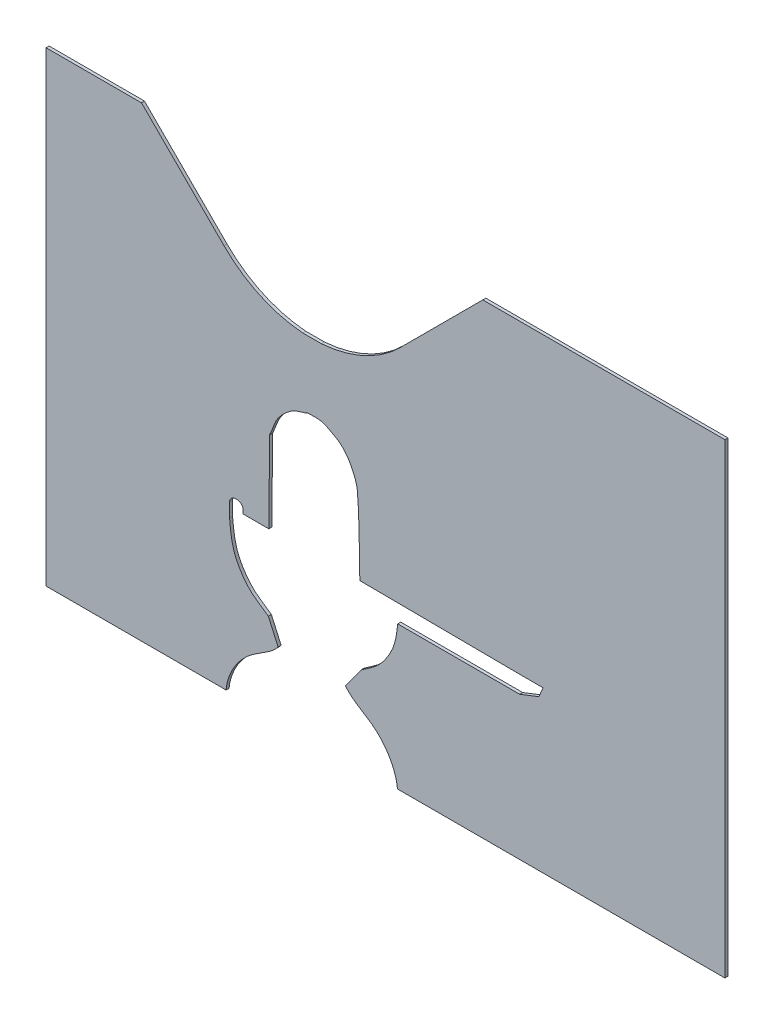
SolidWorks part; units mm, degrees
ref_plane "Front Plane" through (0, 0, 0) normal (0, 0, 1) x (1, 0, 0)
ref_plane "Top Plane" through (0, 0, 0) normal (0, 1, 0) x (1, 0, 0)
ref_plane "Right Plane" through (0, 0, 0) normal (1, 0, 0) x (0, 0, -1)
sketch "Sketch1" plane through (0, 0, 0) normal (0, 0, 1) x (1, 0, 0)
  line L0 (133.3333, 254.5) -> (666.6667, 254.5) construction
  line L1 (133.3333, 254.5) -> (666.6667, 254.5) construction
  line L2 (370.4976, 301.8562) -> (372, 438)
  line L3 (522, 303) -> (789, 301)
  line L5 (584.6436, 11.5928) -> (537.0464, 5.228)
  line L6 (537.0464, 5.228) -> (347.0464, 5.228)
  line L7 (347.0464, 5.228) -> (299.4492, 11.5928)
  line L10 (788.0464, 272.228) -> (585.1554, 272.228)
  line L11 (305.2792, 294.7179) -> (305.2792, 307.6224)
  line L15 (305.2792, 294.7179) -> (305.2792, 284.7179)
  line L22 (788.0464, 272.228) -> (819.9189, 284.7179)
  line L23 (819.9189, 284.7179) -> (827.0328, 301)
  line L24 (827.0328, 301) -> (789, 301)
  line L25 (369.7697, 175.6281) -> (386.0962, 139.3042)
  line L27 (315.2792, 317.6224) -> (317.682, 317.6224)
  line L28 (524.0902, 175.3163) -> (497.9967, 139.3042)
  line L29 (447, 5.228) -> (447, 123.3402) construction
  line L30 (327.682, 307.6224) -> (327.682, 301.8562)
  line L31 (327.682, 301.8562) -> (370.4976, 301.8562)
  line L34 (444.2405, 428) -> (444.2405, 446.7948) construction
  arc A8 (406.6112, 432.934) -> (481.8698, 432.934) centre (444.2405, 573.9572) ccw
  arc A9 (317.682, 317.6224) -> (327.682, 307.6224) centre (317.682, 307.6224) cw
  arc A10 (406.6112, 418.489) -> (481.8698, 418.489) centre (444.2405, 573.9572) ccw
  arc A11 (305.2792, 307.6224) -> (315.2792, 317.6224) centre (315.2792, 307.6224) cw
  arc A12 (406.6112, 432.934) -> (406.6112, 418.489) centre (408.5979, 425.7115) ccw
  arc A13 (481.8698, 432.934) -> (481.8698, 418.489) centre (479.8831, 425.7115) cw
  arc A15 (406.6112, 398) -> (481.8698, 398) centre (444.2405, 539.0232) ccw
  arc A16 (406.6112, 383.5551) -> (481.8698, 383.5551) centre (444.2405, 539.0232) ccw
  arc A17 (406.6112, 398) -> (406.6112, 383.5551) centre (408.5979, 390.7775) ccw
  arc A18 (481.8698, 398) -> (481.8698, 383.5551) centre (479.8831, 390.7775) cw
  arc A19 (406.6112, 363.066) -> (481.8698, 363.066) centre (444.2405, 504.0892) ccw
  arc A20 (406.6112, 348.6211) -> (481.8698, 348.6211) centre (444.2405, 504.0892) ccw
  arc A21 (406.6112, 363.066) -> (406.6112, 348.6211) centre (408.5979, 355.8435) ccw
  arc A22 (481.8698, 363.066) -> (481.8698, 348.6211) centre (479.8831, 355.8435) cw
  spline S0 degree 3 poles (497.9967, 139.3042) (511.7518, 122.1516) (533.2072, 114.7602) (549.1688, 100.4046) (557.8006, 92.6413) (565.3882, 83.5064) (571.3127, 73.5225) (576.9673, 63.9934) (581.1463, 53.4194) (583.4781, 42.5871) (585.6538, 32.4799) (584.2551, 21.9242) (584.6436, 11.5928) knots -0.601085 -0.601085 -0.601085 -0.601085 1 1 1 2 2 2 3 3 3 4 4 4 4
  spline S6 degree 3 poles (524.0902, 175.3163) (534.1328, 182.777) (545.3011, 188.9678) (553.9879, 197.958) (562.3903, 206.6539) (569.2318, 216.9804) (574.5688, 227.831) (581.2804, 241.4764) (583.659, 256.9216) (585.1554, 272.228) knots 0.030911 0.030911 0.030911 0.030911 1 1 1 2 2 2 2.820582 2.820582 2.820582 2.820582
  spline S9 degree 3 poles (372, 438) (377.0706, 448.1412) (379.4614, 459.737) (386, 469) (392.1182, 477.6674) (400.1437, 485.1586) (409, 491) (416.1323, 495.7043) (425.0671, 496.8268) (433, 500) (433.4377, 500.1751) (433.5288, 501.0152) (434, 501) (438.4944, 500.855) (456.988, 503.3404) (466, 498) (474.3605, 493.0456) (483.7936, 489.5201) (491, 483) (498.0695, 476.6038) (503.6725, 468.4948) (508, 460) (512.7848, 450.6076) (517.0638, 440.4993) (518, 430) (521.7619, 387.8131) (520.6667, 345.3333) (522, 303) knots 0 0 0 0 1 1 1 2 2 2 3 3 3 4 4 4 5 5 5 6 6 6 7 7 7 8 8 8 9 9 9 9
  spline S13 degree 3 poles (369.7697, 175.6281) (359.276, 183.4916) (347.4468, 189.8334) (338.2886, 199.2185) (329.7041, 208.0157) (322.698, 218.4783) (317.2186, 229.4811) (308.8213, 246.3434) (306.9517, 265.9548) (305.2792, 284.7179) knots 0 0 0 0 1 1 1 2 2 2 3 3 3 3
  spline S20 degree 3 poles (386.0962, 139.3042) (372.341, 122.1516) (350.8856, 114.7602) (334.924, 100.4046) (326.2922, 92.6413) (318.7046, 83.5064) (312.7801, 73.5225) (307.1255, 63.9934) (302.9465, 53.4194) (300.6147, 42.5871) (298.4391, 32.4799) (299.8377, 21.9242) (299.4492, 11.5928) knots -0.601085 -0.601085 -0.601085 -0.601085 1 1 1 2 2 2 3 3 3 4 4 4 4
  point P21 (320.0752, 796.7868)
  point P22 (444.2405, 639.4617)
  point P24 (385.3282, 418.6761)
  point P25 (503.1529, 418.6761)
  point P27 (560.9295, 796.7868)
  point P31 (440.5024, 886.2654)
  point P36 (315.1479, 786.7868)
  point P37 (440.5024, 886.2654)
  point P38 (568.9564, 790.8228)
  dimension "D2" = 3
  dimension "D4" = 10
  dimension "D5" = 10
extrude "Boss-Extrude1" add sketch "Sketch1" against normal blind 5
sketch "Sketch4" plane through (0, 0, 0) normal (0, 0, 1) x (1, 0, 0)
  line L0 (442.6877, 501.3599) -> (442.6877, 672.663) construction
  line L1 (0, 809.9054) -> (158.6896, 809.9054)
  line L2 (0, 809.9054) -> (0, 34.0489)
  line L3 (0, 34.0489) -> (1129.4723, 34.0489)
  line L4 (1129.4723, 809.9054) -> (1129.4723, 34.0489)
  line L5 (589.4434, 672.663) -> (726.6858, 809.9054)
  line L6 (295.932, 672.663) -> (158.6896, 809.9054)
  line L7 (726.6858, 809.9054) -> (1129.4723, 809.9054)
  line L8 (427.2747, 612.4479) -> (458.1007, 612.4479)
  line L10 (347.0464, 34.0489) -> (537.0464, 34.0489) construction
  arc A0 (295.932, 672.663) -> (427.2747, 612.4479) centre (442.6877, 819.4187) ccw
  arc A1 (458.1007, 612.4479) -> (589.4434, 672.663) centre (442.6877, 819.4187) ccw
  spline S0 degree 3 poles (522, 303) (520.6667, 345.3333) (521.7619, 387.8131) (518, 430) (517.0638, 440.4993) (512.7848, 450.6076) (508, 460) (503.6725, 468.4948) (498.0695, 476.6038) (491, 483) (483.7936, 489.5201) (474.3605, 493.0456) (466, 498) (456.988, 503.3404) (438.4944, 500.855) (434, 501) (433.5288, 501.0152) (433.4377, 500.1751) (433, 500) (425.0671, 496.8268) (416.1323, 495.7043) (409, 491) (400.1437, 485.1586) (392.1182, 477.6674) (386, 469) (379.4614, 459.737) (377.0706, 448.1412) (372, 438) knots 0 0 0 0 1 1 1 2 2 2 3 3 3 4 4 4 5 5 5 6 6 6 7 7 7 8 8 8 9 9 9 9 construction
extrude "Boss-Extrude2" add sketch "Sketch4" against normal blind 5 separate body
surface "Surface-Offset1" parameters "D1"=0
other "SurfaceCut1"
sketch "Sketch5" plane through (0, 0, -5) normal (0, 0, -1) x (-1, 0, 0)
  line L16 (-305.2792, 294.7179) -> (-305.2792, 307.6224)
  line L17 (-305.2792, 284.7179) -> (-305.2792, 294.7179)
  line L18 (-386.0962, 139.3042) -> (-369.7697, 175.6281)
  line L19 (-347.0464, 5.228) -> (-299.4492, 11.5928)
  line L20 (-537.0464, 5.228) -> (-347.0464, 5.228)
  line L21 (-584.6436, 11.5928) -> (-537.0464, 5.228)
  line L22 (-524.0902, 175.3163) -> (-497.9967, 139.3042)
  line L23 (-788.0464, 272.228) -> (-585.1554, 272.228)
  line L24 (-819.9189, 284.7179) -> (-788.0464, 272.228)
  line L25 (-827.0328, 301) -> (-819.9189, 284.7179)
  line L26 (-789, 301) -> (-827.0328, 301)
  line L27 (-522, 303) -> (-789, 301)
  line L28 (-370.4976, 301.8562) -> (-372, 438)
  line L29 (-327.682, 301.8562) -> (-370.4976, 301.8562)
  line L30 (-327.682, 307.6224) -> (-327.682, 301.8562)
  line L31 (-315.2792, 317.6224) -> (-317.682, 317.6224)
  line L32 (-305.2792, 294.7179) -> (-305.2792, 307.6224)
  line L33 (-305.2792, 284.7179) -> (-305.2792, 294.7179)
  line L34 (-386.0962, 139.3042) -> (-369.7697, 175.6281)
  line L35 (-347.0464, 5.228) -> (-299.4492, 11.5928)
  line L36 (-537.0464, 5.228) -> (-347.0464, 5.228)
  line L37 (-584.6436, 11.5928) -> (-537.0464, 5.228)
  line L38 (-524.0902, 175.3163) -> (-497.9967, 139.3042)
  line L39 (-788.0464, 272.228) -> (-585.1554, 272.228)
  line L40 (-819.9189, 284.7179) -> (-788.0464, 272.228)
  line L41 (-827.0328, 301) -> (-819.9189, 284.7179)
  line L42 (-789, 301) -> (-827.0328, 301)
  line L43 (-522, 303) -> (-789, 301)
  line L44 (-370.4976, 301.8562) -> (-372, 438)
  line L45 (-327.682, 301.8562) -> (-370.4976, 301.8562)
  line L46 (-327.682, 307.6224) -> (-327.682, 301.8562)
  line L47 (-315.2792, 317.6224) -> (-317.682, 317.6224)
  arc A2 (-317.682, 317.6224) -> (-327.682, 307.6224) centre (-317.682, 307.6224) ccw
  arc A3 (-305.2792, 307.6224) -> (-315.2792, 317.6224) centre (-315.2792, 307.6224) ccw
  arc A20 (-317.682, 317.6224) -> (-327.682, 307.6224) centre (-317.682, 307.6224) ccw
  arc A21 (-305.2792, 307.6224) -> (-315.2792, 317.6224) centre (-315.2792, 307.6224) ccw
  spline S5 degree 3 poles (1370.3465, -2257.936) (-692.3965, 262.3678) (-416.9117, 118.6475) (-338.2886, 199.2185) (-329.7041, 208.0157) (-322.698, 218.4783) (-317.2186, 229.4811) (-245.5601, 373.3746) (-649.2551, 717.4686) (2405.6564, -973.8479) knots -7.58501 -7.58501 -7.58501 -7.58501 1 1 1 2 2 2 10.533469 10.533469 10.533469 10.533469 only from (-369.7697, 175.6281) to (-305.2792, 284.7179)
  spline S6 degree 3 poles (2692.1293, 140.7772) (-545.2452, -172.9535) (-281.2426, -47.4074) (-300.6147, 42.5871) (-302.9465, 53.4194) (-307.1255, 63.9934) (-312.7801, 73.5225) (-318.7046, 83.5064) (-326.2922, 92.6413) (-334.924, 100.4046) (-424.7448, 181.1878) (-688.5348, 41.4385) (1224.8452, 2661.5843) knots -8.505081 -8.505081 -8.505081 -8.505081 0.398915 0.398915 0.398915 1.398915 1.398915 1.398915 2.398915 2.398915 2.398915 11.408703 11.408703 11.408703 11.408703 only from (-299.4492, 11.5928) to (-386.0962, 139.3042)
  spline S7 degree 3 poles (-2108.8793, 2661.5039) (-195.5635, 41.4413) (-459.349, 181.187) (-549.1688, 100.4046) (-557.8006, 92.6413) (-565.3882, 83.5064) (-571.3127, 73.5225) (-576.9673, 63.9934) (-581.1463, 53.4194) (-583.4781, 42.5871) (-602.8503, -47.4078) (-338.8451, -172.9547) (-3576.2683, 140.7816) knots -8.009696 -8.009696 -8.009696 -8.009696 1 1 1 2 2 2 3 3 3 11.904039 11.904039 11.904039 11.904039 only from (-497.9967, 139.3042) to (-584.6436, 11.5928)
  spline S8 degree 3 poles (-3303.9197, -967.3183) (-241.6126, 709.6073) (-644.7099, 370.4341) (-574.5688, 227.831) (-569.2318, 216.9804) (-562.3903, 206.6539) (-553.9879, 197.958) (-476.6455, 117.9141) (-202.5869, 259.7807) (-2277.7838, -2248.4875) knots -7.724113 -7.724113 -7.724113 -7.724113 0.851493 0.851493 0.851493 1.851493 1.851493 1.851493 10.479734 10.479734 10.479734 10.479734 only from (-585.1554, 272.228) to (-524.0902, 175.3163)
  spline S9 degree 3 poles (2354.1299, 1677.7005) (-541.3375, 177.2794) (-334.372, 395.8604) (-386, 469) (-392.1182, 477.6674) (-400.1437, 485.1586) (-409, 491) (-416.1323, 495.7043) (-425.0671, 496.8268) (-433, 500) (-433.4377, 500.1751) (-433.5288, 501.0152) (-434, 501) (-438.4944, 500.855) (-456.988, 503.3404) (-466, 498) (-474.3605, 493.0456) (-483.7936, 489.5201) (-491, 483) (-498.0695, 476.6038) (-503.6725, 468.4948) (-508, 460) (-512.7848, 450.6076) (-517.0638, 440.4993) (-518, 430) (-547.9548, 94.0784) (-269.9465, -260.4086) (-3362.2994, -411.7164) knots -6.895915 -6.895915 -6.895915 -6.895915 1 1 1 2 2 2 3 3 3 4 4 4 5 5 5 6 6 6 7 7 7 8 8 8 15.962695 15.962695 15.962695 15.962695 only from (-372, 438) to (-522, 303)
  spline S10 degree 3 poles (-369.7697, 175.6281) (-359.276, 183.4916) (-347.4468, 189.8334) (-338.2886, 199.2185) (-329.7041, 208.0157) (-322.698, 218.4783) (-317.2186, 229.4811) (-308.8213, 246.3434) (-306.9517, 265.9548) (-305.2792, 284.7179) knots 0 0 0 0 1 1 1 2 2 2 3 3 3 3
  spline S11 degree 3 poles (-299.4492, 11.5928) (-299.8377, 21.9242) (-298.4391, 32.4799) (-300.6147, 42.5871) (-302.9465, 53.4194) (-307.1255, 63.9934) (-312.7801, 73.5225) (-318.7046, 83.5064) (-326.2922, 92.6413) (-334.924, 100.4046) (-350.8856, 114.7602) (-372.341, 122.1516) (-386.0962, 139.3042) knots -0.601085 -0.601085 -0.601085 -0.601085 0.398915 0.398915 0.398915 1.398915 1.398915 1.398915 2.398915 2.398915 2.398915 4 4 4 4
  spline S12 degree 3 poles (-497.9967, 139.3042) (-511.7518, 122.1516) (-533.2072, 114.7602) (-549.1688, 100.4046) (-557.8006, 92.6413) (-565.3882, 83.5064) (-571.3127, 73.5225) (-576.9673, 63.9934) (-581.1463, 53.4194) (-583.4781, 42.5871) (-585.6538, 32.4799) (-584.2551, 21.9242) (-584.6436, 11.5928) knots -0.601085 -0.601085 -0.601085 -0.601085 1 1 1 2 2 2 3 3 3 4 4 4 4
  spline S13 degree 3 poles (-585.1554, 272.228) (-583.659, 256.9216) (-581.2804, 241.4764) (-574.5688, 227.831) (-569.2318, 216.9804) (-562.3903, 206.6539) (-553.9879, 197.958) (-545.3011, 188.9678) (-534.1328, 182.777) (-524.0902, 175.3163) knots 0.030911 0.030911 0.030911 0.030911 0.851493 0.851493 0.851493 1.851493 1.851493 1.851493 2.820582 2.820582 2.820582 2.820582
  spline S14 degree 3 poles (-372, 438) (-377.0706, 448.1412) (-379.4614, 459.737) (-386, 469) (-392.1182, 477.6674) (-400.1437, 485.1586) (-409, 491) (-416.1323, 495.7043) (-425.0671, 496.8268) (-433, 500) (-433.4377, 500.1751) (-433.5288, 501.0152) (-434, 501) (-438.4944, 500.855) (-456.988, 503.3404) (-466, 498) (-474.3605, 493.0456) (-483.7936, 489.5201) (-491, 483) (-498.0695, 476.6038) (-503.6725, 468.4948) (-508, 460) (-512.7848, 450.6076) (-517.0638, 440.4993) (-518, 430) (-521.7619, 387.8131) (-520.6667, 345.3333) (-522, 303) knots 0 0 0 0 1 1 1 2 2 2 3 3 3 4 4 4 5 5 5 6 6 6 7 7 7 8 8 8 9 9 9 9
  dimension "D3" = 0
extrude "Cut-Extrude1" cut sketch "Sketch5" against normal blind 10
